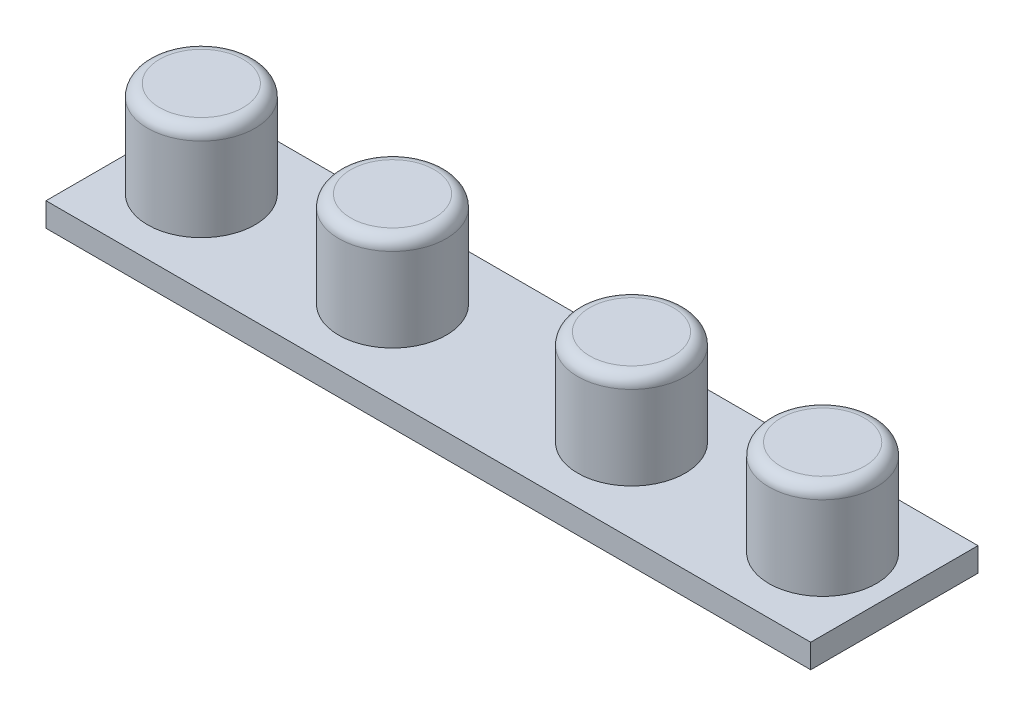
SolidWorks part; units mm, degrees
ref_plane "Front Plane" through (0, 0, 0) normal (0, 0, 1) x (1, 0, 0)
ref_plane "Top Plane" through (0, 0, 0) normal (0, 1, 0) x (1, 0, 0)
ref_plane "Right Plane" through (0, 0, 0) normal (1, 0, 0) x (0, 0, -1)
sketch "Sketch1" plane through (0, 0, 0) normal (0, 1, 0) x (1, 0, 0)
  line L1 (-16, 3.5) -> (16, 3.5)
  line L2 (-16, 3.5) -> (-16, -3.5)
  line L3 (-16, -3.5) -> (16, -3.5)
  line L4 (16, 3.5) -> (16, -3.5)
  line L5 (-16, 3.5) -> (16, -3.5) construction
  line L6 (-16, -3.5) -> (16, 3.5) construction
  point P0 (0, 0)
  dimension "D1" = 32
  dimension "D2" = 7
extrude "Boss-Extrude1" add sketch "Sketch1" along normal blind 1
sketch "Sketch2" plane through (0, 1, 0) normal (0, 1, 0) x (1, 0, 0)
  circle A0 centre (-13, 0) radius 2.25
  circle A1 centre (-5, 0) radius 2.25
  circle A2 centre (5, 0) radius 2.25
  circle A3 centre (13, 0) radius 2.25
  dimension "D1" = 4.5
  dimension "D2" = 4.5
  dimension "D3" = 4.5
  dimension "D4" = 4.5
  dimension "D5" = 8
  dimension "D6" = 10
  dimension "D7" = 8
  dimension "D8" = 5
extrude "Boss-Extrude2" add sketch "Sketch2" along normal blind 4
fillet "Fillet1" radius 0.5 4 edges at (13, 5, 2.25) (5, 5, 2.25) (-5, 5, 2.25) (-13, 5, 2.25)
